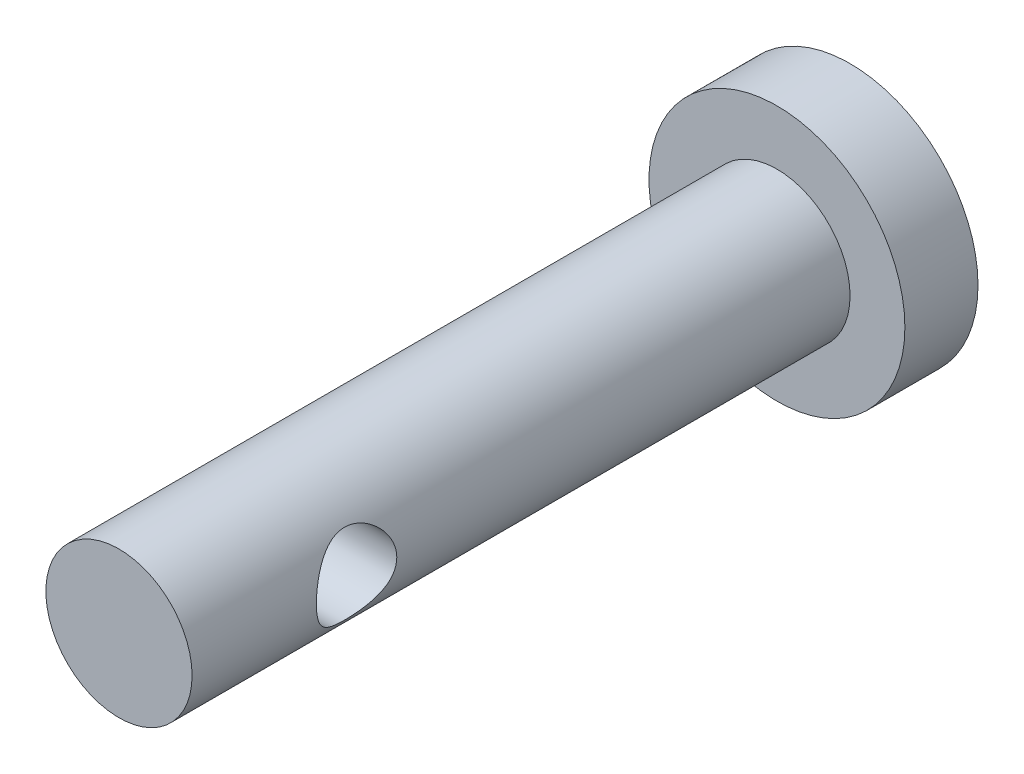
SolidWorks part; units mm, degrees
ref_plane "Płaszczyzna przednia" through (0, 0, 0) normal (0, 0, 1) x (1, 0, 0)
ref_plane "Płaszczyzna górna" through (0, 0, 0) normal (0, 1, 0) x (1, 0, 0)
ref_plane "Płaszczyzna prawa" through (0, 0, 0) normal (1, 0, 0) x (0, 0, -1)
sketch "Szkic1" plane through (0, 0, 0) normal (0, 0, 1) x (1, 0, 0)
  circle A0 centre (0, 0) radius 3.5
extrude "Dodanie-wyciągnięcie1" add sketch "Szkic1" along normal blind 2
sketch "Szkic2" plane through (0, 0, 2) normal (0, 0, 1) x (1, 0, 0)
  circle A0 centre (0, 0) radius 2
extrude "Dodanie-wyciągnięcie2" add sketch "Szkic2" along normal blind 18
ref_plane "Płaszczyzna1" through (-2, 0, 0) normal (-1, 0, 0) x (0, 0, 1)
sketch "Szkic3" plane through (-2, 0, 0) normal (-1, 0, 0) x (0, 0, 1)
  line L0 (2, -2) -> (2, 2) construction
  circle A0 centre (15.5, 0) radius 1.1
  dimension "D1" = 13.5
extrude "Wytnij-wyciągnięcie1" cut sketch "Szkic3" against normal through all
